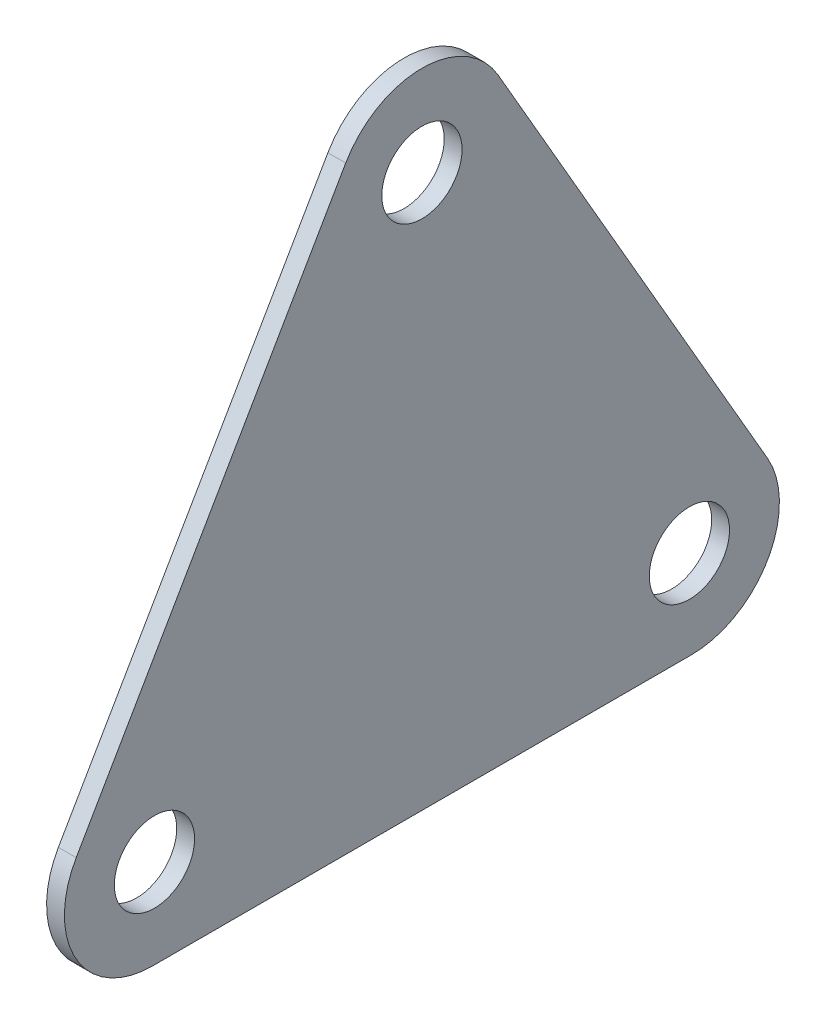
SolidWorks part; units mm, degrees
ref_plane "Front Plane" through (0, 0, 0) normal (0, 0, 1) x (1, 0, 0)
ref_plane "Top Plane" through (0, 0, 0) normal (0, 1, 0) x (1, 0, 0)
ref_plane "Right Plane" through (0, 0, 0) normal (1, 0, 0) x (0, 0, -1)
sketch "Sketch1" plane through (0, 0, 0) normal (1, 0, 0) x (0, 0, -1)
  line L0 (-13.6567, 0) -> (16.3433, 0) construction
  line L1 (16.3433, 0) -> (1.3433, 25.9808) construction
  line L2 (1.3433, 25.9808) -> (-13.6567, 0) construction
  line L3 (-13.7703, -5) -> (16.4569, -5)
  line L4 (20.7302, 2.4016) -> (5.6166, 28.5791)
  line L5 (-2.93, 28.5791) -> (-18.0436, 2.4016)
  line L6 (-22.317, -5) -> (25.0035, -5) construction
  line L7 (25.0035, -5) -> (1.3433, 35.9808) construction
  line L8 (1.3433, 35.9808) -> (-22.317, -5) construction
  circle A0 centre (-13.6567, 0) radius 2.25
  circle A1 centre (16.3433, 0) radius 2.25
  circle A2 centre (1.3433, 25.9808) radius 2.25
  arc A3 (16.4569, -5) -> (20.7302, 2.4016) centre (16.4569, -0.0656) ccw
  arc A4 (5.6166, 28.5791) -> (-2.93, 28.5791) centre (1.3433, 26.1119) ccw
  arc A5 (-18.0436, 2.4016) -> (-13.7703, -5) centre (-13.7703, -0.0656) ccw
  dimension "D3" = 4.5
  dimension "D4" = 4.9344
  dimension "D1" = 30
  dimension "D2" = 5
extrude "Boss-Extrude1" add sketch "Sketch1" along normal blind 1
